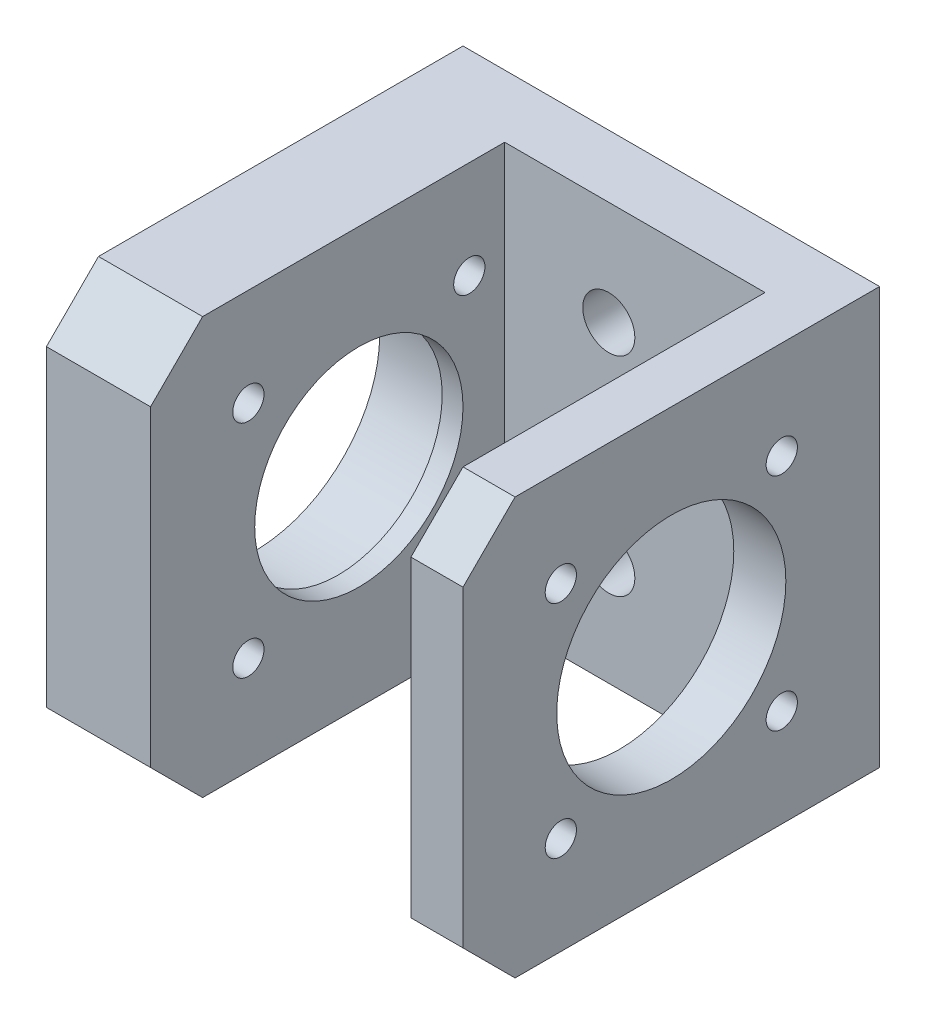
SolidWorks part; units mm, degrees
material "6061 合金"
ref_plane "前基準面" through (0, 0, 0) normal (0, 0, 1) x (1, 0, 0)
ref_plane "上基準面" through (0, 0, 0) normal (0, 1, 0) x (1, 0, 0)
ref_plane "右基準面" through (0, 0, 0) normal (1, 0, 0) x (0, 0, -1)
sketch "草圖1" plane through (0, 0, 0) normal (0, 0, 1) x (1, 0, 0)
  line L1 (-20, -20) -> (20, -20)
  line L2 (-20, -20) -> (-20, 20)
  line L3 (-20, 20) -> (20, 20)
  line L4 (20, -20) -> (20, 20)
  line L5 (-20, -20) -> (20, 20) construction
  line L6 (-20, 20) -> (20, -20) construction
  point P0 (0, 0)
  dimension "D1" = 40
  dimension "D2" = 40
extrude "填料-伸長1" add sketch "草圖1" along normal blind 40
sketch "草圖2" plane through (0, 0, 40) normal (0, 0, 1) x (1, 0, 0)
  line L0 (-20, -20) -> (20, -20) construction
  line L1 (20, 20) -> (15, 20)
  line L2 (20, 20) -> (20, -20)
  line L3 (20, -20) -> (15, -20)
  line L4 (15, 20) -> (15, -20)
  line L6 (-20, 20) -> (-10, 20)
  line L7 (-20, 20) -> (-20, -20)
  line L8 (-20, -20) -> (-10, -20)
  line L9 (-10, 20) -> (-10, -20)
  line M6 (20, 20) -> (-20, 20)
  line M8 (-20, -20) -> (20, -20)
  dimension "D1" = 5
  dimension "D2" = 10
extrude "除料-伸長1" cut sketch "草圖2" against normal blind 34 contours L9 L4 M6 M8
sketch "草圖3" plane through (0, 0, 6) normal (0, 0, 1) x (1, 0, 0)
  line L0 (0, -10) -> (0, 10) construction
  circle A0 centre (0, 10) radius 2.5
  circle A1 centre (0, -10) radius 2.5
  point P4 (0, 0)
  dimension "D2" = 5
  dimension "D1" = 20
extrude "除料-伸長2" cut sketch "草圖3" against normal through all
chamfer "導角1" distance 5 angle 45 4 edges at (-15, -20, 40) (17.5, -20, 40) (17.5, 20, 40) (-15, 20, 40)
sketch "草圖4" plane through (20, 0, 0) normal (1, 0, 0) x (0, 0, -1)
  line L0 (-40, 0) -> (0, 0) construction
  line L2 (-40, -15) -> (-40, 15) construction
  line L3 (0, -20) -> (0, 20) construction
  circle A0 centre (-20, 0) radius 11
  dimension "D1" = 22
sketch "草圖5" plane through (-20, 0, 0) normal (-1, 0, 0) x (0, 0, 1)
  line L0 (40, 0) -> (0, 0) construction
  line L1 (40, 15) -> (40, -15) construction
  circle A0 centre (20, 0) radius 12
  dimension "D1" = 24
extrude "除料-伸長4" cut sketch "草圖5" against normal blind 8
sketch "草圖7" plane through (-12, 0, 0) normal (-1, 0, 0) x (0, 0, 1)
  circle A0 centre (20, 0) radius 10
  dimension "D1" = 20
extrude "除料-伸長5" cut sketch "草圖7" against normal up to next
extrude "除料-伸長6" cut sketch "草圖4" against normal up to next
sketch "草圖9" plane through (20, 0, 0) normal (1, 0, 0) x (0, 0, -1)
  line L0 (-20, 0) -> (-9.3934, 10.6066) construction
  line L1 (-35, -20) -> (0, -20) construction
  circle A1 centre (-9.3934, 10.6066) radius 1.5
  dimension "D3" = 3
  dimension "D1" = 15
  dimension "D2" = 45
extrude "除料-伸長7" cut sketch "草圖9" against normal through all
pattern_circular "環狀複製排列1" count 4 every 90 about axis through (0, 0, 20) along (1, 0, 0) of "除料-伸長7"
